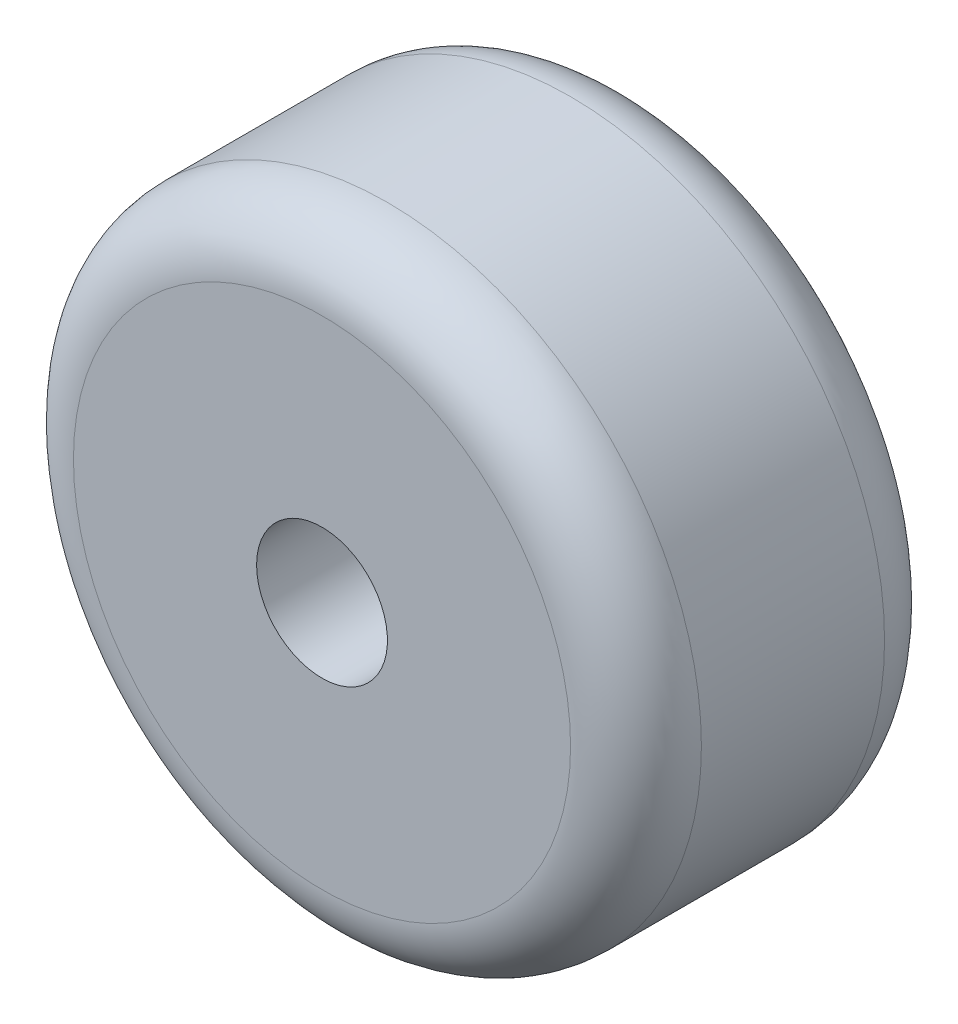
SolidWorks part; units mm, degrees
ref_plane "Ebene vorne" through (0, 0, 0) normal (0, 0, 1) x (1, 0, 0)
ref_plane "Ebene oben" through (0, 0, 0) normal (0, 1, 0) x (1, 0, 0)
ref_plane "Ebene rechts" through (0, 0, 0) normal (1, 0, 0) x (0, 0, -1)
sketch "Skizze1" plane through (0, 0, 0) normal (0, 0, 1) x (1, 0, 0)
  circle A0 centre (0, 0) radius 24
  dimension "D1" = 48
extrude "Aufsatz-Linear austragen1" add sketch "Skizze1" along normal blind 24
fillet "Verrundung1" radius 5 2 edges at (24, 0, 0) (24, 0, 24)
sketch "Skizze2" plane through (0, 0, 0) normal (0, 0, -1) x (-1, 0, 0)
  circle A0 centre (0, 0) radius 5
  dimension "D1" = 10
extrude "Schnitt-Linear austragen1" cut sketch "Skizze2" against normal through all
